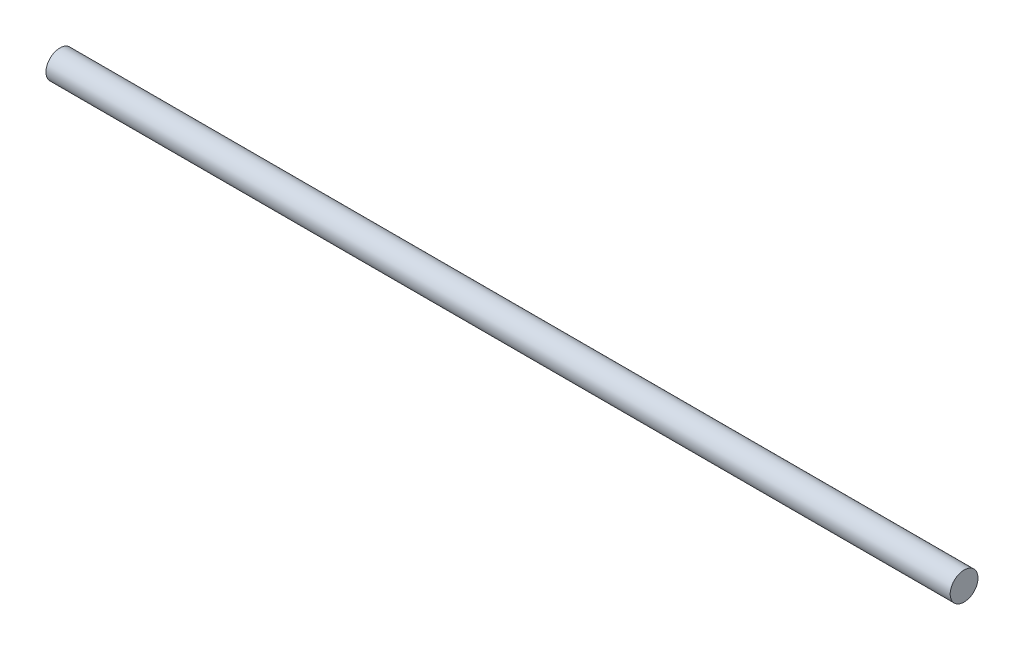
SolidWorks part; units mm, degrees
ref_plane "Front Plane" through (0, 0, 0) normal (0, 0, 1) x (1, 0, 0)
ref_plane "Top Plane" through (0, 0, 0) normal (0, 1, 0) x (1, 0, 0)
ref_plane "Right Plane" through (0, 0, 0) normal (1, 0, 0) x (0, 0, -1)
sketch "Sketch1" plane through (0, 0, 0) normal (1, 0, 0) x (0, 0, -1)
  circle A0 centre (0, 0) radius 1
  dimension "D1" = 2
extrude "Boss-Extrude1" add sketch "Sketch1" along normal mid plane 65
